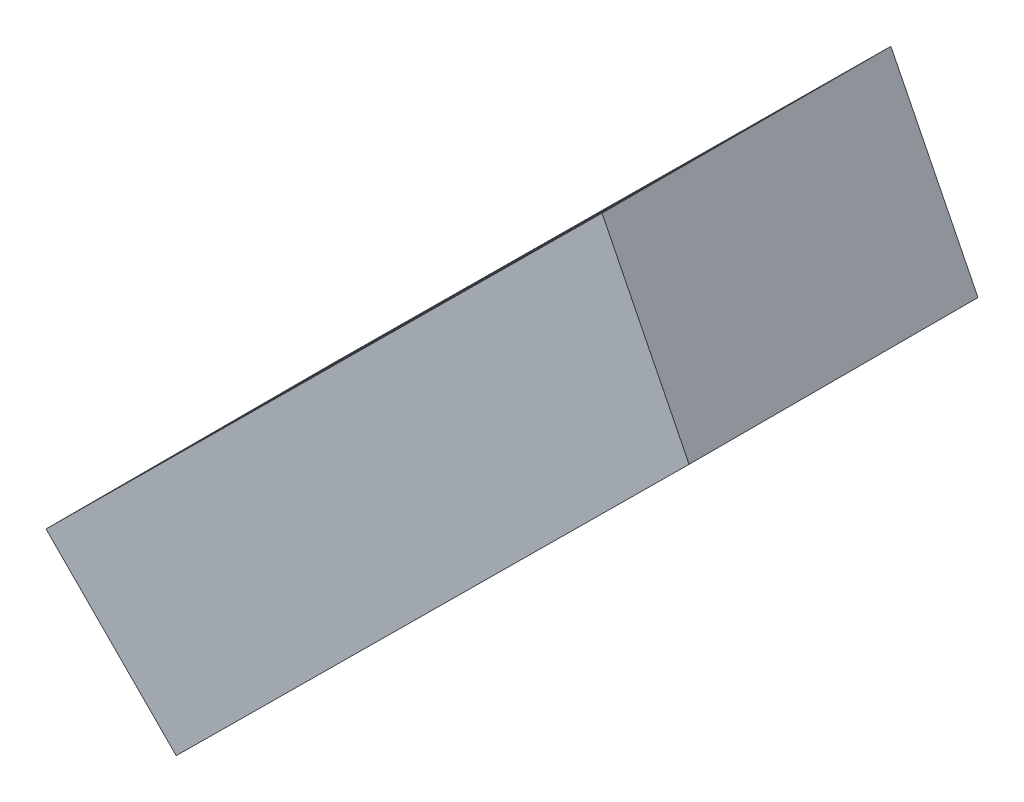
SolidWorks part; units mm, degrees
ref_plane "Alzado" through (0, 0, 0) normal (0, 0, 1) x (1, 0, 0)
ref_plane "Planta" through (0, 0, 0) normal (0, 1, 0) x (1, 0, 0)
ref_plane "Vista lateral" through (0, 0, 0) normal (1, 0, 0) x (0, 0, -1)
ref_plane "Plane1" through (0, 0, -0.375) normal (0, 0, -1) x (-1, 0, 0)
sketch "Sketch1" plane through (0, 0, -0.375) normal (0, 0, -1) x (-1, 0, 0)
  line L0 (1.8321, 1.1888) -> (1.6813, 0.8877)
  line L1 (1.6813, 0.8877) -> (2.5691, 0.0071)
  line L2 (2.5691, 0.0071) -> (2.7944, 0.2343)
  line L3 (2.7944, 0.2343) -> (1.8321, 1.1888)
  dimension "D1" = 0.1508
  dimension "D2" = 0.8878
  dimension "D3" = 1.1131
  dimension "D4" = 0.2272
  dimension "D5" = 0.8806
  dimension "D6" = 1.1818
extrude "Boss-Extrude1" add sketch "Sketch1" against normal blind 0.5
